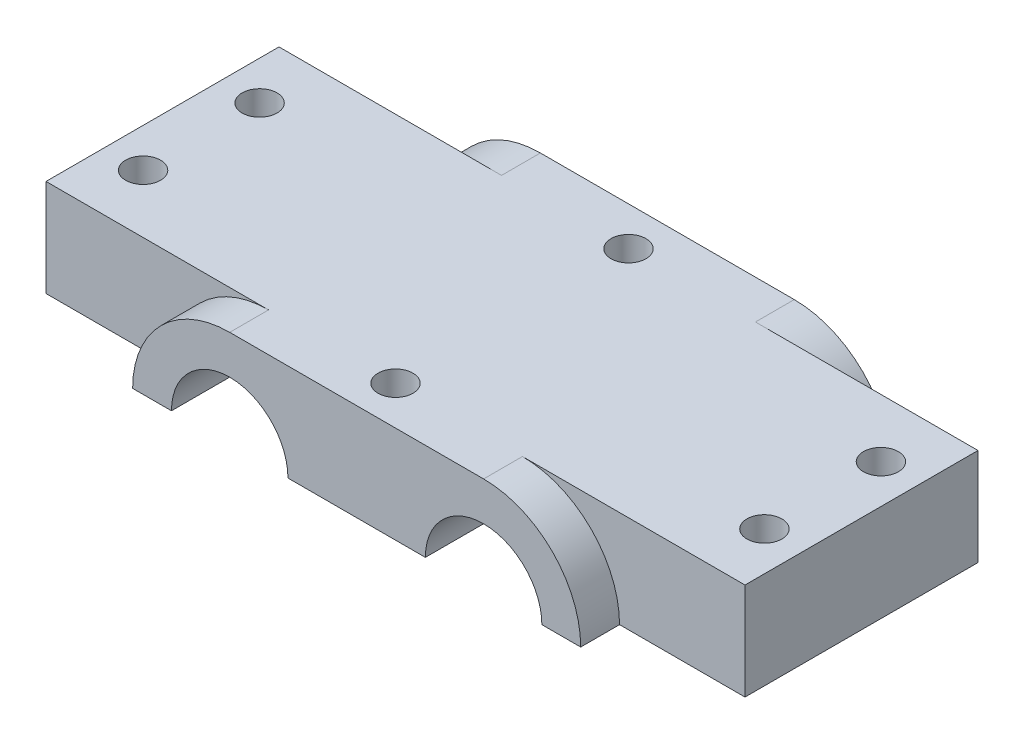
SolidWorks part; units mm, degrees
ref_plane "Front Plane" through (0, 0, 0) normal (0, 0, 1) x (1, 0, 0)
ref_plane "Top Plane" through (0, 0, 0) normal (0, 1, 0) x (1, 0, 0)
ref_plane "Right Plane" through (0, 0, 0) normal (1, 0, 0) x (0, 0, -1)
sketch "Sketch1" plane through (0, 0, 0) normal (0, 1, 0) x (1, 0, 0)
  line L1 (45, -15) -> (-45, -15)
  line L2 (45, -15) -> (45, 15)
  line L3 (45, 15) -> (-45, 15)
  line L4 (-45, -15) -> (-45, 15)
  line L5 (45, -15) -> (-45, 15) construction
  line L6 (45, 15) -> (-45, -15) construction
  point P0 (0, 0)
  dimension "D1" = 30
  dimension "D2" = 90
extrude "Boss-Extrude1" add sketch "Sketch1" along normal mid plane 12.5
sketch "Sketch3" plane through (0, 0, 15) normal (0, 0, 1) x (1, 0, 0)
  line L0 (-45, -6.25) -> (45, -6.25) construction
  line L1 (0, 0) -> (0, 19.8194) construction
  line L2 (-45, 6.25) -> (45, 6.25) construction
  line L3 (-28.8459, -6.25) -> (-23.8459, -6.25)
  line L4 (-16.3459, 6.25) -> (16.3459, 6.25)
  line L6 (-8.8459, -6.25) -> (8.8459, -6.25)
  line L7 (23.8459, -6.25) -> (28.8459, -6.25)
  arc A0 (-8.8459, -6.25) -> (-23.8459, -6.25) centre (-16.3459, -6.25) ccw
  arc A1 (-16.3459, 6.25) -> (-28.8459, -6.25) centre (-16.3459, -6.25) ccw
  arc A2 (8.8459, -6.25) -> (23.8459, -6.25) centre (16.3459, -6.25) cw
  arc A3 (16.3459, 6.25) -> (28.8459, -6.25) centre (16.3459, -6.25) cw
  dimension "D1" = 25
  dimension "D2" = 15
  dimension "D3" = 17.5
extrude "Boss-Extrude3" add sketch "Sketch3" along normal blind 5
mirror "Mirror1" about plane through (0, 0, 0) normal (0, 0, 1) of "Boss-Extrude3"
sketch "Sketch5" plane through (0, 0, 15) normal (0, 0, 1) x (1, 0, 0)
  line L1 (-23.8459, -6.25) -> (-8.8459, -6.25)
  line L2 (-23.8459, -6.25) -> (-8.8459, -6.25)
  line L3 (8.8459, -6.25) -> (23.8459, -6.25)
  line L4 (8.8459, -6.25) -> (23.8459, -6.25)
  arc A1 (-8.8459, -6.25) -> (-23.8459, -6.25) centre (-16.3459, -6.25) ccw
  arc A2 (-8.8459, -6.25) -> (-23.8459, -6.25) centre (-16.3459, -6.25) ccw
  arc A3 (23.8459, -6.25) -> (8.8459, -6.25) centre (16.3459, -6.25) ccw
  arc A4 (23.8459, -6.25) -> (8.8459, -6.25) centre (16.3459, -6.25) ccw
  dimension "D1" = 0
  dimension "D2" = 0
extrude "Cut-Extrude1" cut sketch "Sketch5" against normal blind 41
sketch "Sketch6" plane through (0, 6.25, 0) normal (0, 1, 0) x (1, 0, 0)
  line L0 (-45, 15) -> (-45, -15) construction
  line L1 (-45, -15) -> (-16.3459, -15) construction
  line L2 (0, 0) -> (0, 24.2119) construction
  line L3 (0, 0) -> (15.9085, 0) construction
  line L4 (16.3459, 20) -> (-16.3459, 20) construction
  circle A0 centre (-40, 7.5) radius 2.25
  circle A1 centre (-40, -7.5) radius 2.25
  circle A2 centre (40, -7.5) radius 2.25
  circle A3 centre (40, 7.5) radius 2.25
  circle A4 centre (0, 15) radius 2.25
  circle A5 centre (0, -15) radius 2.25
  dimension "D1" = 4.5
  dimension "D5" = 4.5
  dimension "D2" = 5
  dimension "D3" = 15
  dimension "D4" = 7.5
  dimension "D6" = 5
extrude "Cut-Extrude2" cut sketch "Sketch6" against normal through all
